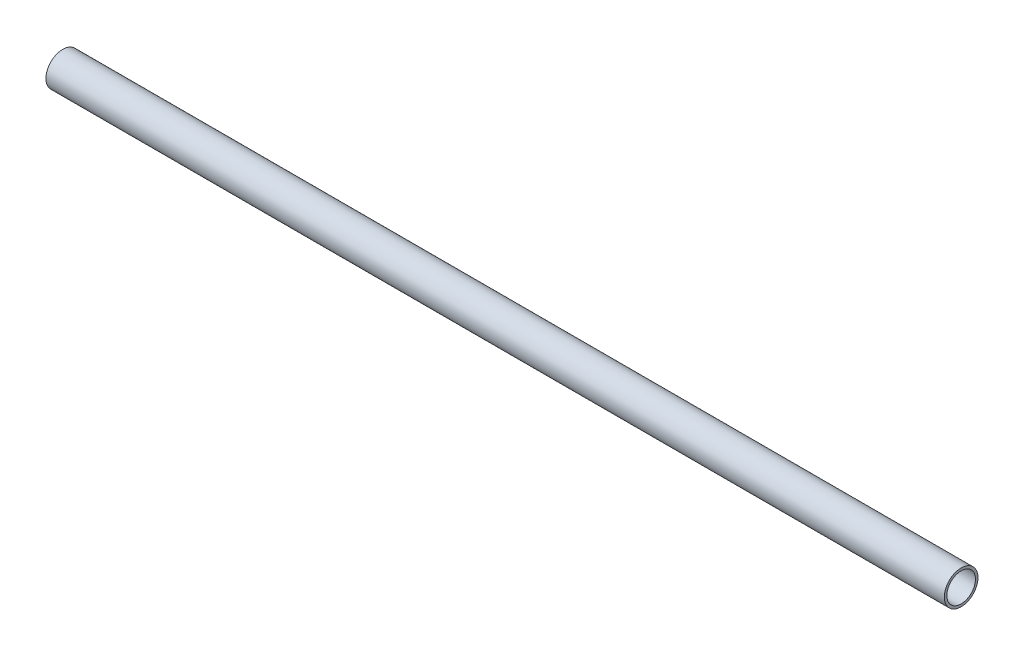
SolidWorks part; units mm, degrees
material "AISI 304"
ref_plane "Front Plane" through (0, 0, 0) normal (0, 0, 1) x (1, 0, 0)
ref_plane "Top Plane" through (0, 0, 0) normal (0, 1, 0) x (1, 0, 0)
ref_plane "Right Plane" through (0, 0, 0) normal (1, 0, 0) x (0, 0, -1)
sketch "Sketch1" plane through (0, 0, 0) normal (1, 0, 0) x (0, 0, -1)
  circle A0 centre (0, 0) radius 4.0513
  circle A1 centre (0, 0) radius 4.7625
  dimension "D1" = 9.525
  dimension "D2" = 0.7112
extrude "Boss-Extrude1" add sketch "Sketch1" along normal mid plane 254
sketch "Sketch2" plane through (0, 0, 0) normal (0, 1, 0) x (1, 0, 0)
  circle A0 centre (-112.5, 0) radius 3.175
  circle A1 centre (-37.5, 0) radius 3.175
  circle A2 centre (37.5, 0) radius 3.175
  circle A3 centre (112.5, 0) radius 3.175
  dimension "D1" = 6.35
  dimension "D2" = 75
  dimension "D3" = 75
  dimension "D4" = 75
  dimension "D5" = 37.5
extrude "Cut-Extrude1" cut sketch "Sketch2" against normal through all
